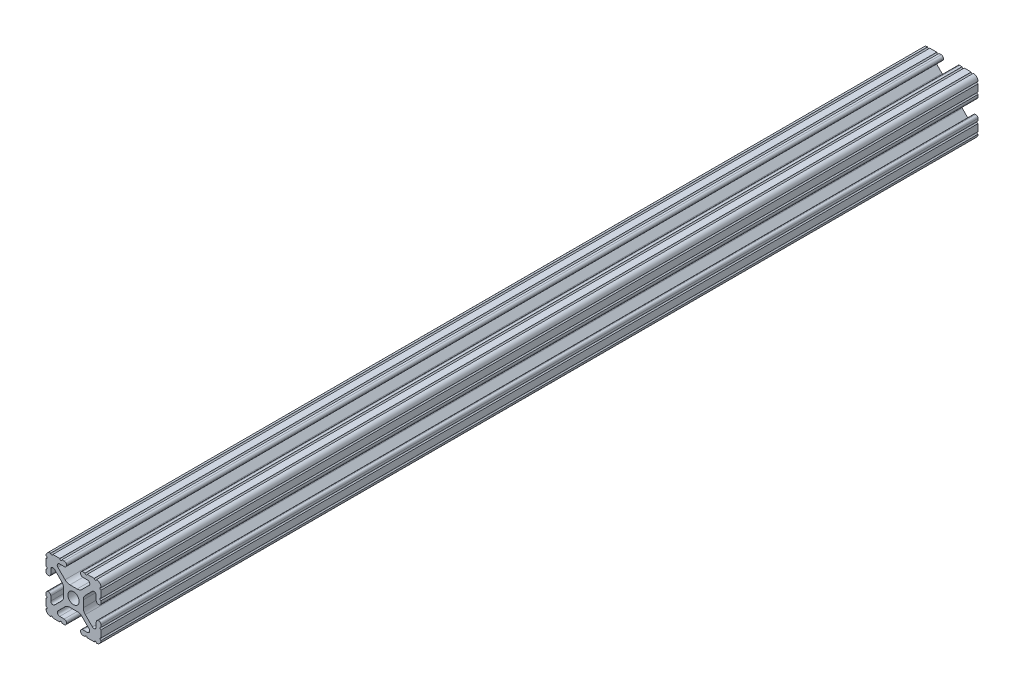
SolidWorks part; units mm, degrees
material "6105-T5 Aluminum"
ref_plane "Front Plane" through (0, 0, 0) normal (0, 0, 1) x (1, 0, 0)
ref_plane "Top Plane" through (0, 0, 0) normal (0, 1, 0) x (1, 0, 0)
ref_plane "Right Plane" through (0, 0, 0) normal (1, 0, 0) x (0, 0, -1)
sketch "Sketch1" plane through (0, 0, 0) normal (0, 0, 1) x (1, 0, 0)
  line L0 (-7.207, 8.7244) -> (-3.8983, 5.4232)
  line L1 (-4.2875, 10.4902) -> (-6.4768, 10.4902)
  line L2 (-3.2385, 11.651) -> (-3.2385, 11.5392)
  line L3 (-5.3171, 12.7) -> (-4.2875, 12.7)
  line L4 (0, 13.4005) -> (0, -14.8534) construction
  line L5 (12.7, 0) -> (-13.9989, 0) construction
  line L6 (-9.5504, 12.7) -> (-6.3331, 12.7)
  line L7 (-12.7, 6.3331) -> (-12.7, 9.5504)
  line L8 (-12.7, 4.2875) -> (-12.7, 5.3171)
  line L9 (-11.5392, 3.2385) -> (-11.651, 3.2385)
  line L10 (-10.4902, 6.4021) -> (-10.4902, 4.2875)
  line L11 (-5.441, 3.8408) -> (-8.7371, 7.1294)
  line L12 (-4.5085, -1.5932) -> (-4.5085, 1.5932)
  line L13 (-1.7093, -4.4958) -> (1.7093, -4.4958)
  line L14 (3.9523, -5.4237) -> (7.1797, -8.6452)
  line L15 (6.4164, -10.4902) -> (4.2875, -10.4902)
  line L16 (3.2385, -11.5392) -> (3.2385, -11.651)
  line L17 (4.2875, -12.7) -> (5.3171, -12.7)
  line L18 (6.3331, -12.7) -> (9.5504, -12.7)
  line L19 (12.7, -9.5504) -> (12.7, -6.3331)
  line L20 (12.7, -5.3171) -> (12.7, -4.2875)
  line L21 (11.651, -3.2385) -> (11.5392, -3.2385)
  line L22 (10.4902, -4.2875) -> (10.4902, -6.4021)
  line L23 (8.7371, -7.1294) -> (5.441, -3.8408)
  line L24 (4.5085, -1.5932) -> (4.5085, 1.5932)
  line L25 (5.441, 3.8408) -> (8.7371, 7.1294)
  line L26 (10.4902, 6.4021) -> (10.4902, 4.2875)
  line L27 (11.5392, 3.2385) -> (11.651, 3.2385)
  line L28 (12.7, 4.2875) -> (12.7, 5.3171)
  line L29 (12.7, 6.3331) -> (12.7, 9.5504)
  line L30 (9.5504, 12.7) -> (6.3331, 12.7)
  line L31 (5.3171, 12.7) -> (4.2875, 12.7)
  line L32 (3.2385, 11.651) -> (3.2385, 11.5392)
  line L33 (4.2875, 10.4902) -> (6.4768, 10.4902)
  line L34 (7.207, 8.7244) -> (3.8983, 5.4232)
  line L35 (1.6558, 4.4958) -> (-1.6558, 4.4958)
  line L36 (-8.7371, -7.1294) -> (-5.441, -3.8408)
  line L37 (-10.4902, -4.2875) -> (-10.4902, -6.4021)
  line L38 (-11.651, -3.2385) -> (-11.5392, -3.2385)
  line L39 (-12.7, -5.3171) -> (-12.7, -4.2875)
  line L40 (-12.7, -9.5504) -> (-12.7, -6.3331)
  line L41 (-6.3331, -12.7) -> (-9.5504, -12.7)
  line L42 (-4.2875, -12.7) -> (-5.3171, -12.7)
  line L43 (-3.2385, -11.5392) -> (-3.2385, -11.651)
  line L44 (-6.4164, -10.4902) -> (-4.2875, -10.4902)
  line L45 (-3.9523, -5.4237) -> (-7.1797, -8.6452)
  arc A0 (-7.207, 8.7244) -> (-6.4768, 10.4902) centre (-6.4768, 9.4563) cw
  arc A1 (-3.2385, 11.5392) -> (-4.2875, 10.4902) centre (-4.2875, 11.5392) cw
  arc A2 (-4.2875, 12.7) -> (-3.2385, 11.651) centre (-4.2875, 11.651) cw
  arc A3 (-5.3171, 12.7) -> (-6.3331, 12.7) centre (-5.8251, 12.7) cw
  arc A4 (-9.5504, 12.7) -> (-10.5664, 12.6998) centre (-10.0584, 12.7) cw
  arc A5 (-12.6998, 10.5664) -> (-10.5664, 12.6998) centre (-10.5918, 10.5918) cw
  arc A6 (-12.6998, 10.5664) -> (-12.7, 9.5504) centre (-12.7, 10.0584) cw
  arc A7 (-12.7, 6.3331) -> (-12.7, 5.3171) centre (-12.7, 5.8251) cw
  arc A8 (-11.651, 3.2385) -> (-12.7, 4.2875) centre (-11.651, 4.2875) cw
  arc A9 (-10.4902, 4.2875) -> (-11.5392, 3.2385) centre (-11.5392, 4.2875) cw
  circle A10 centre (0, 0) radius 2.6035
  arc A11 (-10.4902, 6.4021) -> (-8.7371, 7.1294) centre (-9.4628, 6.4021) cw
  arc A12 (-5.441, 3.8408) -> (-4.5085, 1.5932) centre (-7.6835, 1.5932) cw
  arc A13 (-4.5085, -1.5932) -> (-5.441, -3.8408) centre (-7.6835, -1.5932) cw
  arc A14 (-8.7371, -7.1294) -> (-10.4902, -6.4021) centre (-9.4628, -6.4021) cw
  arc A15 (-1.7093, -4.4958) -> (-3.9523, -5.4237) centre (-1.7093, -7.6708) ccw
  arc A16 (3.9523, -5.4237) -> (1.7093, -4.4958) centre (1.7093, -7.6708) ccw
  arc A17 (6.4164, -10.4902) -> (7.1797, -8.6452) centre (6.4164, -9.4098) ccw
  arc A18 (4.2875, -10.4902) -> (3.2385, -11.5392) centre (4.2875, -11.5392) ccw
  arc A19 (3.2385, -11.651) -> (4.2875, -12.7) centre (4.2875, -11.651) ccw
  arc A20 (6.3331, -12.7) -> (5.3171, -12.7) centre (5.8251, -12.7) ccw
  arc A21 (10.5664, -12.6998) -> (9.5504, -12.7) centre (10.0584, -12.7) ccw
  arc A22 (10.5664, -12.6998) -> (12.6998, -10.5664) centre (10.5918, -10.5918) ccw
  arc A23 (12.7, -9.5504) -> (12.6998, -10.5664) centre (12.7, -10.0584) ccw
  arc A24 (12.7, -5.3171) -> (12.7, -6.3331) centre (12.7, -5.8251) ccw
  arc A25 (12.7, -4.2875) -> (11.651, -3.2385) centre (11.651, -4.2875) ccw
  arc A26 (11.5392, -3.2385) -> (10.4902, -4.2875) centre (11.5392, -4.2875) ccw
  arc A27 (8.7371, -7.1294) -> (10.4902, -6.4021) centre (9.4628, -6.4021) ccw
  arc A28 (4.5085, -1.5932) -> (5.441, -3.8408) centre (7.6835, -1.5932) ccw
  arc A29 (5.441, 3.8408) -> (4.5085, 1.5932) centre (7.6835, 1.5932) ccw
  arc A30 (10.4902, 6.4021) -> (8.7371, 7.1294) centre (9.4628, 6.4021) ccw
  arc A31 (10.4902, 4.2875) -> (11.5392, 3.2385) centre (11.5392, 4.2875) ccw
  arc A32 (11.651, 3.2385) -> (12.7, 4.2875) centre (11.651, 4.2875) ccw
  arc A33 (12.7, 6.3331) -> (12.7, 5.3171) centre (12.7, 5.8251) ccw
  arc A34 (12.6998, 10.5664) -> (12.7, 9.5504) centre (12.7, 10.0584) ccw
  arc A35 (12.6998, 10.5664) -> (10.5664, 12.6998) centre (10.5918, 10.5918) ccw
  arc A36 (9.5504, 12.7) -> (10.5664, 12.6998) centre (10.0584, 12.7) ccw
  arc A37 (5.3171, 12.7) -> (6.3331, 12.7) centre (5.8251, 12.7) ccw
  arc A38 (4.2875, 12.7) -> (3.2385, 11.651) centre (4.2875, 11.651) ccw
  arc A39 (3.2385, 11.5392) -> (4.2875, 10.4902) centre (4.2875, 11.5392) ccw
  arc A40 (7.207, 8.7244) -> (6.4768, 10.4902) centre (6.4768, 9.4563) ccw
  arc A41 (1.6558, 4.4958) -> (3.8983, 5.4232) centre (1.6558, 7.6708) ccw
  arc A42 (-1.6558, 4.4958) -> (-3.8983, 5.4232) centre (-1.6558, 7.6708) cw
  arc A43 (-11.5392, -3.2385) -> (-10.4902, -4.2875) centre (-11.5392, -4.2875) cw
  arc A44 (-12.7, -4.2875) -> (-11.651, -3.2385) centre (-11.651, -4.2875) cw
  arc A45 (-12.7, -5.3171) -> (-12.7, -6.3331) centre (-12.7, -5.8251) cw
  arc A46 (-12.7, -9.5504) -> (-12.6998, -10.5664) centre (-12.7, -10.0584) cw
  arc A47 (-10.5664, -12.6998) -> (-12.6998, -10.5664) centre (-10.5918, -10.5918) cw
  arc A48 (-10.5664, -12.6998) -> (-9.5504, -12.7) centre (-10.0584, -12.7) cw
  arc A49 (-6.3331, -12.7) -> (-5.3171, -12.7) centre (-5.8251, -12.7) cw
  arc A50 (-3.2385, -11.651) -> (-4.2875, -12.7) centre (-4.2875, -11.651) cw
  arc A51 (-4.2875, -10.4902) -> (-3.2385, -11.5392) centre (-4.2875, -11.5392) cw
  arc A52 (-6.4164, -10.4902) -> (-7.1797, -8.6452) centre (-6.4164, -9.4098) cw
  dimension "D1" = 5.207
  dimension "D9" = 14.859
  dimension "D2" = 25.4
  dimension "D3" = 12.7
  dimension "D4" = 6.477
  dimension "D5" = 8.2042
  dimension "D6" = 9.017
  dimension "D8" = 2.2098
  dimension "D10" = 2.2098
extrude "Extrude1" add sketch "Sketch1" against normal blind 404.8125
equation "\"L\"=15.9375"
equation "\"LENGTH@Extrude1\"=\"L\""
